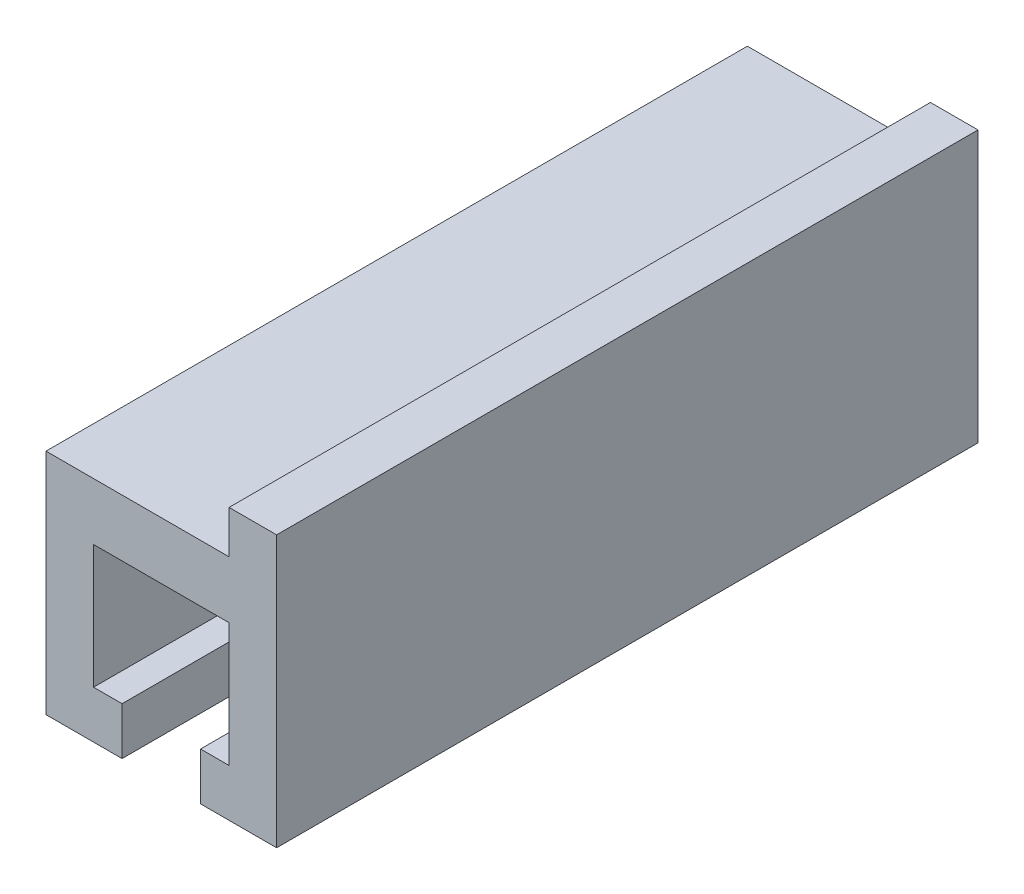
SolidWorks part; units mm, degrees
ref_plane "Front Plane" through (0, 0, 0) normal (0, 0, 1) x (1, 0, 0)
ref_plane "Top Plane" through (0, 0, 0) normal (0, 1, 0) x (1, 0, 0)
ref_plane "Right Plane" through (0, 0, 0) normal (1, 0, 0) x (0, 0, -1)
sketch "Sketch1" plane through (0, 0, 0) normal (0, 0, 1) x (1, 0, 0)
  line L0 (-7.65, 2.6) -> (2.05, 2.6)
  line L1 (2.05, 2.6) -> (2.05, -7)
  line L3 (-7.65, 2.6) -> (-7.65, -7)
  line L4 (-7.65, -7) -> (-4.45, -7)
  line L5 (2.05, -7) -> (-1.15, -7)
  line L6 (-4.45, -7) -> (-4.45, -5)
  line L7 (-4.45, -5) -> (-5.65, -5)
  line L8 (-5.65, -5) -> (-5.65, 0.2)
  line L9 (-5.65, 0.2) -> (0.05, 0.2)
  line L10 (0.05, 0.2) -> (0.05, -5)
  line L11 (0.05, -5) -> (-1.15, -5)
  line L12 (-1.15, -5) -> (-1.15, -7)
  dimension "D2" = 2
  dimension "D3" = 2.4
  dimension "D4" = 2
  dimension "D5" = 5.7
  dimension "D6" = 5.2
  dimension "D8" = 3.3
extrude "Boss-Extrude1" add sketch "Sketch1" along normal blind 29.5
sketch "Sketch2" plane through (0, 0, 29.5) normal (0, 0, 1) x (1, 0, 0)
  line L1 (2.05, 2.6) -> (0.05, 2.6)
  line L2 (2.05, 2.6) -> (2.05, 4.4)
  line L3 (2.05, 4.4) -> (0.05, 4.4)
  line L4 (0.05, 2.6) -> (0.05, 4.4)
  dimension "D1" = 1.8
  dimension "D2" = 2
extrude "Boss-Extrude2" add sketch "Sketch2" against normal blind 29.5
